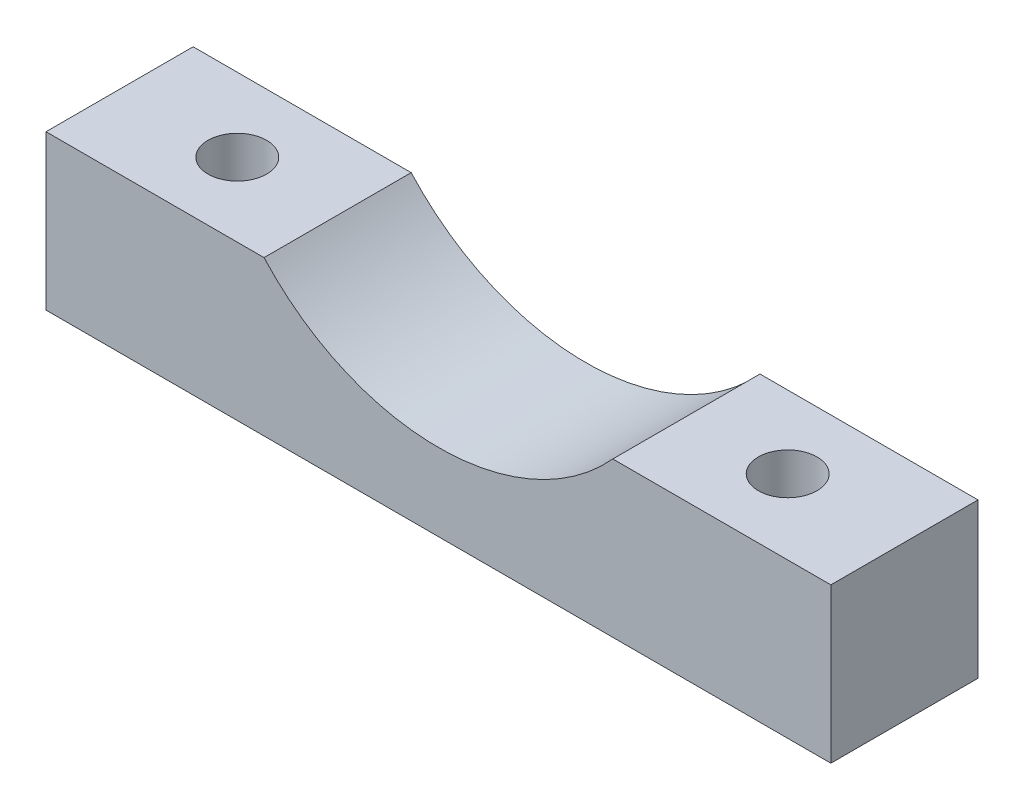
SolidWorks part; units mm, degrees
ref_plane "정면" through (0, 0, 0) normal (0, 0, 1) x (1, 0, 0)
ref_plane "윗면" through (0, 0, 0) normal (0, 1, 0) x (1, 0, 0)
ref_plane "우측면" through (0, 0, 0) normal (1, 0, 0) x (0, 0, -1)
sketch "Sketch1" plane through (0, 0, 0) normal (0, 1, 0) x (1, 0, 0)
  line L1 (0, 0) -> (-50.8, 0)
  line L2 (0, 0) -> (0, 9.525)
  line L3 (0, 9.525) -> (-50.8, 9.525)
  line L4 (-50.8, 0) -> (-50.8, 9.525)
  dimension "D1" = 9.525
  dimension "D2" = 50.8
extrude "Extrude1" add sketch "Sketch1" along normal blind 10
sketch "Sketch2" plane through (0, 0, -9.525) normal (0, 0, -1) x (-1, 0, 0)
  line L0 (0, 5) -> (50.8, 5)
  line L1 (0, 10) -> (0, 0) construction
  line L2 (50.8, 10) -> (50.8, 0) construction
  line L3 (25.4, 5) -> (25.4, 20.24)
  circle A0 centre (25.4, 20.24) radius 15.24
  dimension "D1" = 15.24
extrude "Cut-Extrude1" cut sketch "Sketch2" against normal through all contours A0
ref_plane "Plane1" through (-25, 0, 0) normal (1, 0, 0) x (0, 0, -1)
hole_wizard "CBORE for #6 Socket Head Cap Screw1" positions "3DSketch1" profile "Sketch3" counterbore size "#6" standard "Ansi Inch" end condition through all
sketch3d "3DSketch1"
  line L0 (-50.8, 0, -9.525) -> (-50.8, 0, 0) construction
  line L1 (-50.8, 0, 0) -> (0, 0, 0) construction
  point P0 (-43.18, 0, -4.7625)
  point P2 (-7.6201, 0, -4.826)
  dimension "D1" = 7.62
  dimension "D2" = 4.7625
  dimension "D3" = 4.826
  dimension "D4" = 35.56
sketch "Sketch3" plane through (-43.18, 0, -4.7625) normal (1, 0, 0) x (0, 0, -1)
  line L0 (0, 0) -> (0, 10)
  line L1 (0, 10) -> (1.8986, 10)
  line L3 (1.8986, 10) -> (1.8987, 3.5052)
  line L4 (1.8987, 3.5052) -> (3.5725, 3.5052)
  line L5 (3.5725, 3.5052) -> (3.5725, 0)
  line L7 (3.5725, 0) -> (0, 0)
  line L11 (0, -6.35) -> (0, 107.95) construction
  dimension "Thru Hole Dia." = 3.7973
  dimension "Thru Hole Depth" = 10
  dimension "C'Bore Dia." = 7.145
  dimension "C'Bore Depth" = 3.5052
